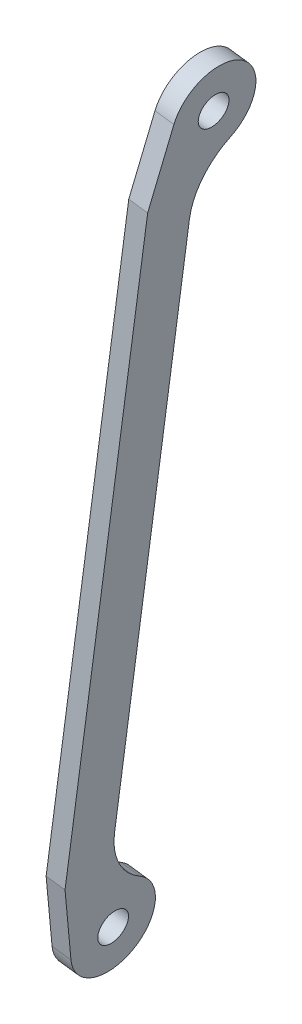
SolidWorks part; units mm, degrees
ref_plane "Front Plane" through (0, 0, 0) normal (0, 0, 1) x (1, 0, 0)
ref_plane "Top Plane" through (0, 0, 0) normal (0, 1, 0) x (1, 0, 0)
ref_plane "Right Plane" through (0, 0, 0) normal (1, 0, 0) x (0, 0, -1)
sketch "Sketch1" plane through (0, 0, 0) normal (0, 1, 0) x (1, 0, 0)
  line L1 (17.1045, -14.8442) -> (183.1045, -14.8442)
  line L2 (-2.2693, -10.7634) -> (17.1045, -14.8442)
  line L3 (183.1045, -14.8442) -> (202.4188, -10.4903)
  line L5 (175.1279, -2.8469) -> (24.7262, -2.8469)
  circle A0 centre (0, 0) radius 4
  circle A2 centre (199.9999, 0.2404) radius 4
  arc A3 (202.4188, -10.4903) -> (190.5657, 5.897) centre (199.9999, 0.2404) ccw
  arc A4 (9.3789, 5.7477) -> (24.7262, -2.8469) centre (24.7262, 15.1531) ccw
  arc A5 (175.1279, -2.8469) -> (190.5657, 5.897) centre (175.1279, 15.1531) ccw
  arc A8 (9.3789, 5.7477) -> (-2.2693, -10.7634) centre (0, 0) ccw
  dimension "D1" = 8
  dimension "D2" = 29
  dimension "D4" = 8
  dimension "D5" = 22
  dimension "D6" = 36
  dimension "D7" = 36
  dimension "D8" = 18
  dimension "D9" = 15.3473
  dimension "D10" = 166
  dimension "D11" = 204.6884
  dimension "D14" = 181.1869
  dimension "D12" = 22
  dimension "D3" = 200
  dimension "D16" = 19.799
  dimension "D17" = 19.799
extrude "Boss-Extrude1" add sketch "Sketch1" along normal blind 5
move or copy body "Body-Move/Copy1" bodies to move or copy 101 copy no rotation origin (99.9999, 2.5, 0) rotation axis (0, 0, 1) rotation angle 82.5
